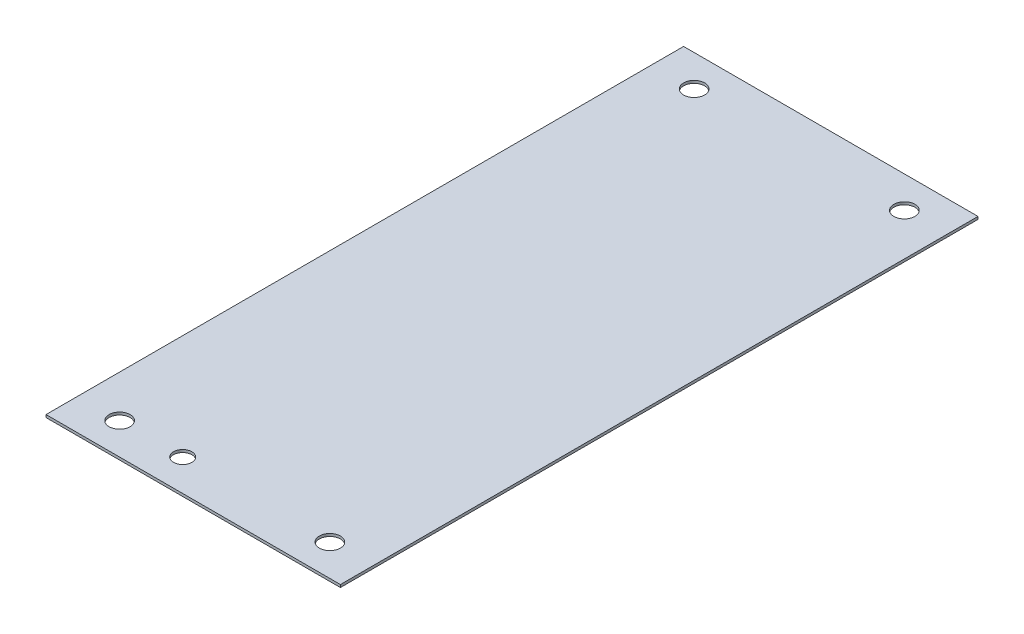
SolidWorks part; units mm, degrees
ref_plane "Front Plane" through (0, 0, 0) normal (0, 0, 1) x (1, 0, 0)
ref_plane "Top Plane" through (0, 0, 0) normal (0, 1, 0) x (1, 0, 0)
ref_plane "Right Plane" through (0, 0, 0) normal (1, 0, 0) x (0, 0, -1)
sketch "Sketch1" plane through (0, 0, 0) normal (0, 1, 0) x (1, 0, 0)
  line L1 (0, 0) -> (355.6, 0)
  line L2 (0, 0) -> (0, 770.128)
  line L3 (0, 770.128) -> (355.6, 770.128)
  line L4 (355.6, 0) -> (355.6, 770.128)
  dimension "D1" = 770.128
  dimension "D2" = 355.6
extrude "Boss-Extrude1" add sketch "Sketch1" along normal blind 3.175
hole_wizard "1 (1) Diameter Hole1" positions "Sketch3" profile "Sketch2" hole size "1" standard "Ansi Inch"
sketch "Sketch3" plane through (0, 3.175, 0) normal (0, 1, 0) x (-1, 0, 0)
  line L0 (0, 0) -> (-355.6, 0) construction
  line L1 (0, -385.064) -> (-355.6, -385.064) construction
  line L2 (0, -770.128) -> (0, 0) construction
  line L3 (-355.6, 0) -> (-355.6, -770.128) construction
  line L4 (-177.8, 0) -> (-177.8, -770.128) construction
  line L5 (-355.6, -770.128) -> (0, -770.128) construction
  point P0 (-50.8, -38.1)
  point P21 (-50.8, -732.028)
  point P23 (-304.8, -732.028)
  point P24 (-304.8, -38.1)
  dimension "D1" = 38.1
  dimension "D2" = 50.8
sketch "Sketch2" plane through (50.8, 3.175, -38.1) normal (1, 0, 0) x (0, 0, 1)
  line L0 (0, 0) -> (0, 28.2049)
  line L1 (0, 28.2049) -> (12.7, 20.574)
  line L2 (12.7, 20.574) -> (12.7, 0)
  line L5 (12.7, 0) -> (0, 0)
  line L10 (0, 28.2049) -> (-12.7, 20.574) construction
  line L11 (0, -6.35) -> (0, 107.95) construction
  dimension "Hole Dia." = 25.4
  dimension "Hole Depth" = 20.574
  dimension "Drill Angle" = 118
sketch "Sketch4" plane through (0, 3.175, 0) normal (0, 1, 0) x (1, 0, 0)
  line L1 (0, 0) -> (355.6, 0) construction
  circle A0 centre (127, 38.1) radius 11.1125
  circle A2 centre (50.8, 38.1) radius 12.7 construction
  dimension "D1" = 38.1
  dimension "D2" = 76.2
extrude "Cut-Extrude1" cut sketch "Sketch4" against normal through all
